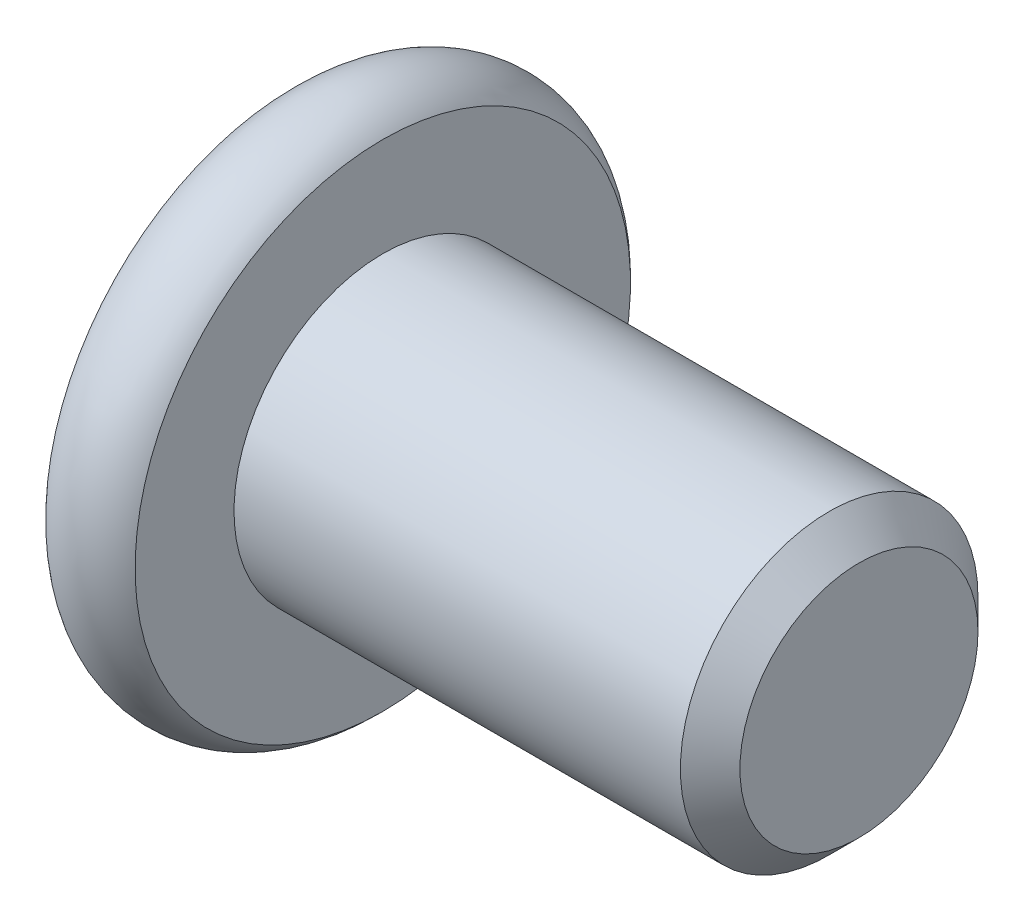
SolidWorks part; units mm, degrees
material "Plain Carbon Steel"
ref_plane "Front Plane" through (0, 0, 0) normal (0, 0, 1) x (1, 0, 0)
ref_plane "Top Plane" through (0, 0, 0) normal (0, 1, 0) x (1, 0, 0)
ref_plane "Right Plane" through (0, 0, 0) normal (1, 0, 0) x (0, 0, -1)
other "M5 x 15"
sketch "Sketch2" plane through (0, 0, 0) normal (1, 0, 0) x (0, 0, -1)
  circle A0 centre (0, 0) radius 2.5
  dimension "D1" = 5
extrude "Boss-Extrude1" add sketch "Sketch2" against normal blind 8
chamfer "Chamfer1" distance 0.5 angle 45 1 edges at (0, 0, -2.5)
sketch "Sketch6" plane through (0, 0, 0) normal (0, 0, 1) x (1, 0, 0)
  line L0 (-9.5, 0) -> (-9.5, 4.1614)
  line L1 (-9.5, 0) -> (-8, 0)
  line L2 (-8.75, 0) -> (-8.75, 3.5) construction
  line L6 (-8, 4.1614) -> (-8, 0)
  line L8 (-8, 0) -> (-14.6471, 0) construction
  line L10 (-8, 2.5) -> (-8, -2.5) construction
  arc A0 (-9.5, 4.1614) -> (-8, 4.1614) centre (-8.75, 3.5) cw
  dimension "D3" = 1
  dimension "D1" = 1.5
  dimension "D2" = 9
revolve "Revolve1" add sketch "Sketch6" angle 360 about L8
sketch "Sketch7" plane through (-9.5, 0, 0) normal (-1, 0, 0) x (0, 0, 1)
  line L1 (0, 1.7321) -> (-1.5, 0.866)
  line L2 (-1.5, 0.866) -> (-1.5, -0.866)
  line L3 (-1.5, -0.866) -> (0, -1.7321)
  line L4 (0, -1.7321) -> (1.5, -0.866)
  line L5 (1.5, -0.866) -> (1.5, 0.866)
  line L6 (1.5, 0.866) -> (0, 1.7321)
  circle A0 centre (0, 0) radius 1.5 construction
  dimension "D1" = 3
extrude "Cut-Extrude1" cut sketch "Sketch7" against normal blind 2.3
sketch "Sketch8" plane through (-9.5, 0, 0) normal (-1, 0, 0) x (0, 0, 1)
  circle A0 centre (0, 0) radius 1.7821
  dimension "D1" = 0.05
extrude "Cut-Extrude2" cut sketch "Sketch8" against normal blind 1 draft 45
